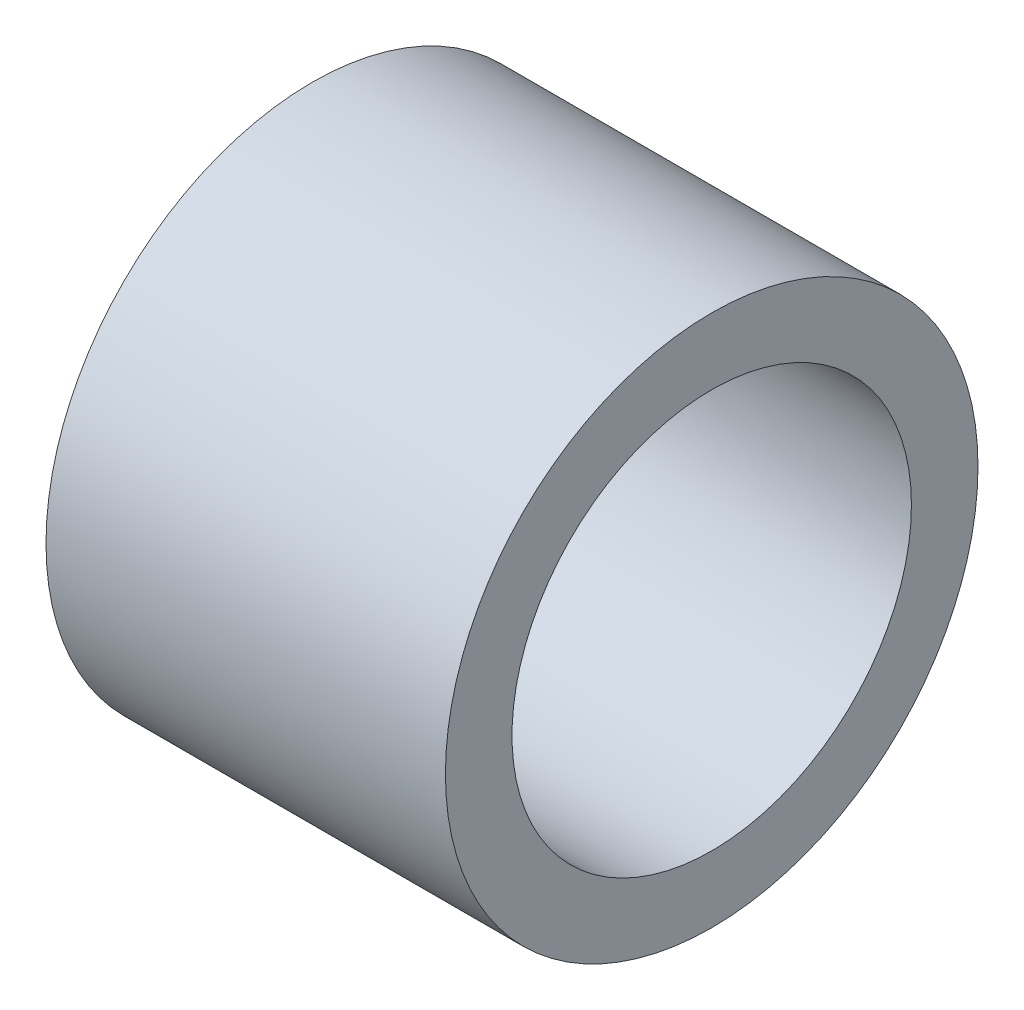
SolidWorks part; units mm, degrees
material "Aluminum Bronze"
ref_plane "Front Plane" through (0, 0, 0) normal (0, 0, 1) x (1, 0, 0)
ref_plane "Top Plane" through (0, 0, 0) normal (0, 1, 0) x (1, 0, 0)
ref_plane "Right Plane" through (0, 0, 0) normal (1, 0, 0) x (0, 0, -1)
sketch "Sketch1" plane through (0, 0, 0) normal (1, 0, 0) x (0, 0, -1)
  circle A0 centre (0, 0) radius 12.7
  circle A1 centre (0, 0) radius 9.525
  dimension "D1" = 25.4
  dimension "D2" = 19.05
extrude "Boss-Extrude1" add sketch "Sketch1" along normal mid plane 19.05
